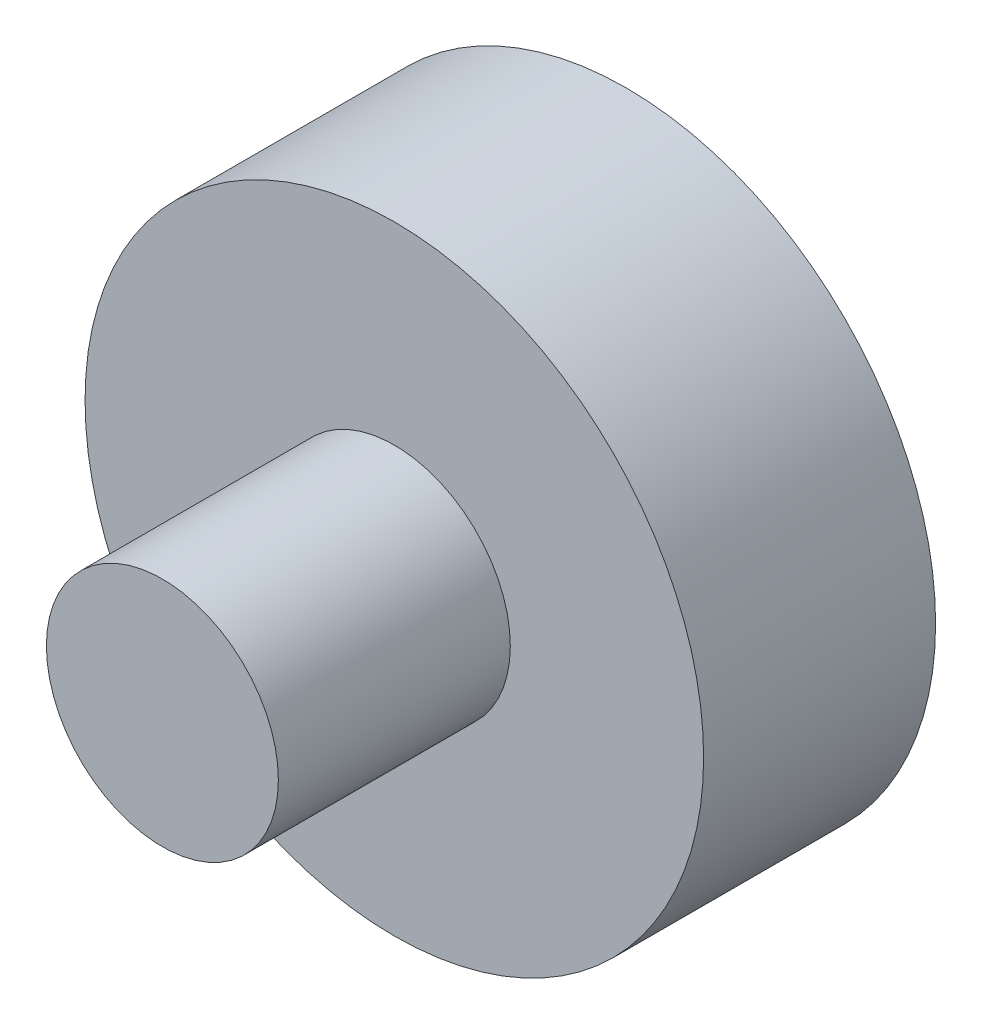
SolidWorks part; units mm, degrees
ref_plane "Front Plane" through (0, 0, 0) normal (0, 0, 1) x (1, 0, 0)
ref_plane "Top Plane" through (0, 0, 0) normal (0, 1, 0) x (1, 0, 0)
ref_plane "Right Plane" through (0, 0, 0) normal (1, 0, 0) x (0, 0, -1)
sketch "Sketch1" plane through (0, 0, 0) normal (0, 0, 1) x (1, 0, 0)
  circle A1 centre (0, 0) radius 25.4
  dimension "D1" = 50.8
extrude "Boss-Extrude1" add sketch "Sketch1" along normal blind 19.05
sketch "Sketch2" plane through (0, 0, 19.05) normal (0, 0, 1) x (1, 0, 0)
  circle A0 centre (0, 0) radius 9.525
  dimension "D1" = 19.05
extrude "Boss-Extrude2" add sketch "Sketch2" along normal blind 19.05
